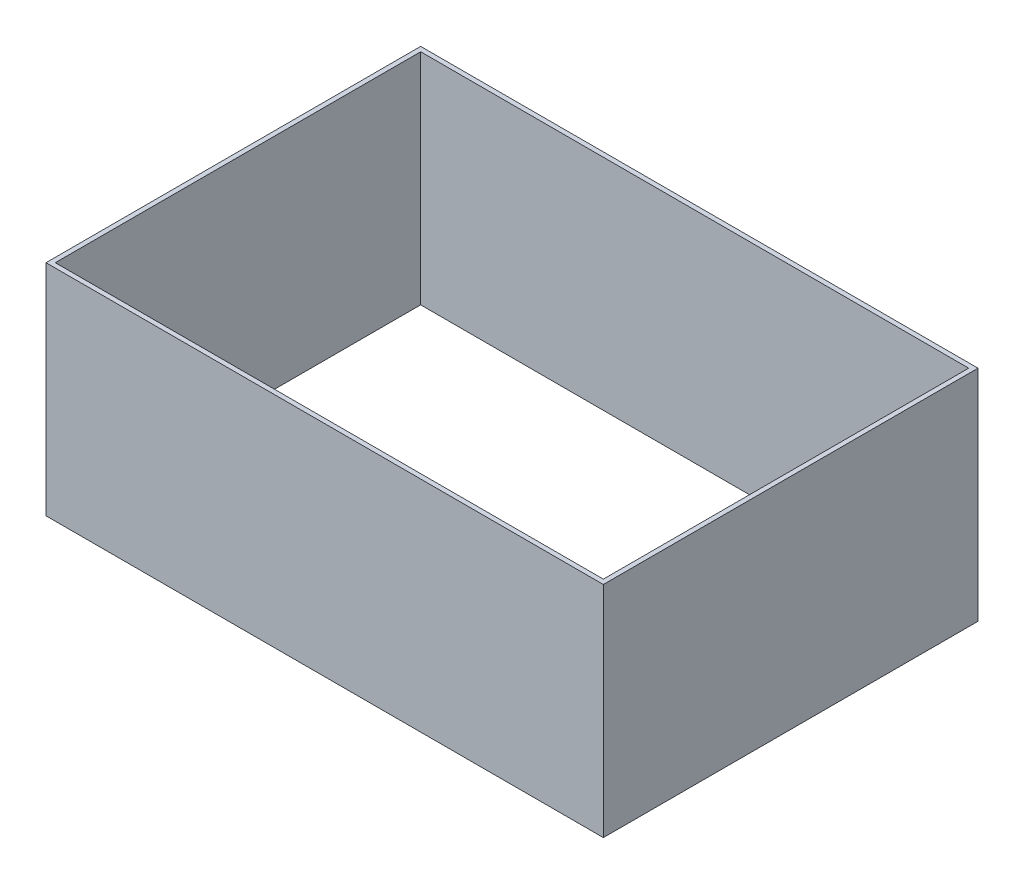
SolidWorks part; units mm, degrees
ref_plane "Front Plane" through (0, 0, 0) normal (0, 0, 1) x (1, 0, 0)
ref_plane "Top Plane" through (0, 0, 0) normal (0, 1, 0) x (1, 0, 0)
ref_plane "Right Plane" through (0, 0, 0) normal (1, 0, 0) x (0, 0, -1)
sketch "Sketch1" plane through (0, 0, 0) normal (0, 1, 0) x (1, 0, 0)
  line L0 (-152.54, 102.54) -> (152.54, 102.54)
  line L1 (-150, 100) -> (150, 100)
  line L2 (-150, 100) -> (-150, -100)
  line L3 (-150, -100) -> (150, -100)
  line L4 (150, 100) -> (150, -100)
  line L5 (-150, 100) -> (150, -100) construction
  line L6 (-150, -100) -> (150, 100) construction
  line L7 (152.54, 102.54) -> (152.54, -102.54)
  line L8 (-152.54, -102.54) -> (152.54, -102.54)
  line L9 (-152.54, 102.54) -> (-152.54, -102.54)
  point P0 (0, 0)
  dimension "D1" = 200
  dimension "D2" = 300
  dimension "D3" = 2.54
extrude "Boss-Extrude1" add sketch "Sketch1" along normal blind 120
